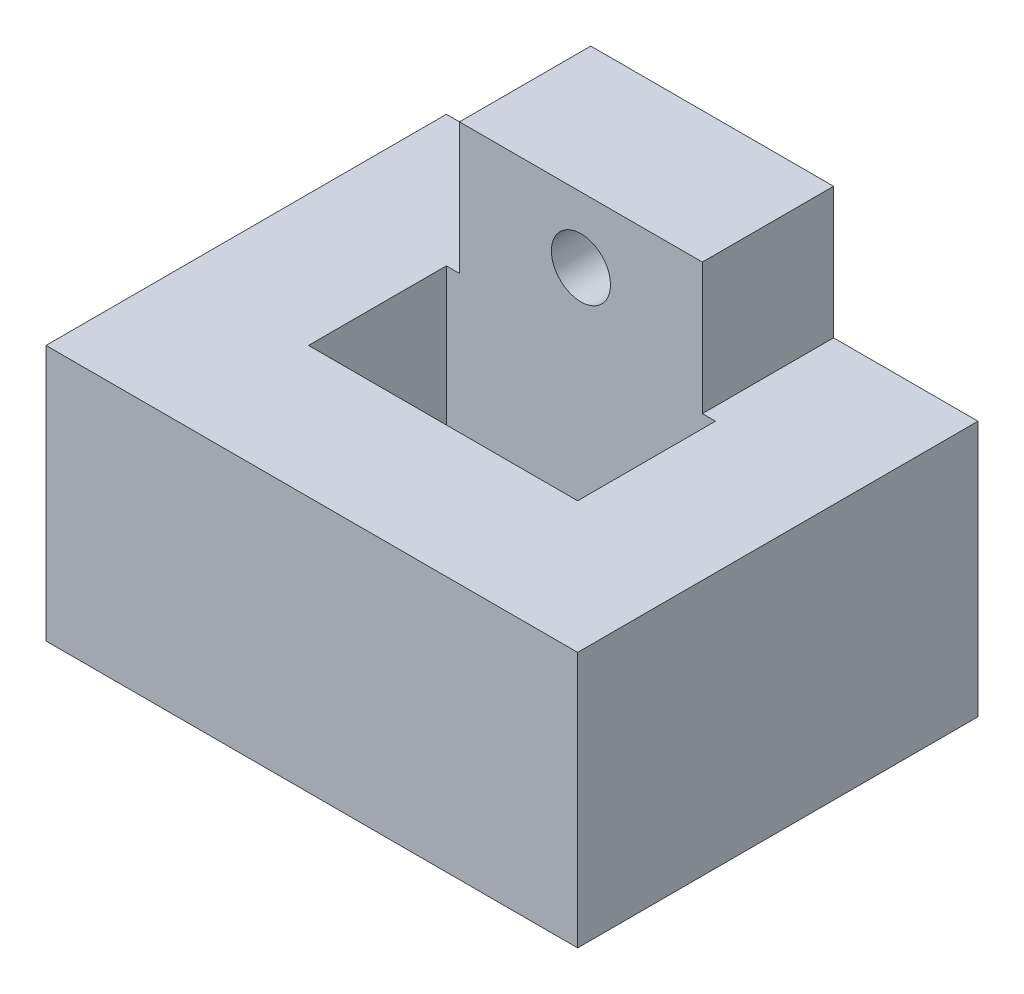
SolidWorks part; units mm, degrees
ref_plane "Front Plane" through (0, 0, 0) normal (0, 0, 1) x (1, 0, 0)
ref_plane "Top Plane" through (0, 0, 0) normal (0, 1, 0) x (1, 0, 0)
ref_plane "Right Plane" through (0, 0, 0) normal (1, 0, 0) x (0, 0, -1)
sketch "Sketch1" plane through (0, 0, 0) normal (0, 1, 0) x (1, 0, 0)
  line L1 (-10.25, 5.25) -> (10.25, 5.25)
  line L2 (-10.25, 5.25) -> (-10.25, -5.25)
  line L3 (-10.25, -5.25) -> (10.25, -5.25)
  line L4 (10.25, 5.25) -> (10.25, -5.25)
  line L5 (-10.25, 5.25) -> (10.25, -5.25) construction
  line L6 (-10.25, -5.25) -> (10.25, 5.25) construction
  line L7 (-20.25, 15.25) -> (20.25, 15.25)
  line L8 (-20.25, 15.25) -> (-20.25, -15.25)
  line L9 (-20.25, -15.25) -> (20.25, -15.25)
  line L10 (20.25, 15.25) -> (20.25, -15.25)
  line L11 (-20.25, 15.25) -> (20.25, -15.25) construction
  line L12 (-20.25, -15.25) -> (20.25, 15.25) construction
  point P0 (0, 0)
  point P6 (0, 0)
  dimension "D1" = 20.5
  dimension "D2" = 10.5
  dimension "D3" = 40.5
  dimension "D4" = 30.5
extrude "Boss-Extrude1" add sketch "Sketch1" along normal blind 19.5
sketch "Sketch4" plane through (0, 0, -15.25) normal (0, 0, 1) x (1, 0, 0)
  line L0 (0, 4.5) -> (0, 0) construction
  line L1 (-20.25, 0) -> (20.25, 0) construction
  circle A0 centre (0, 4.5) radius 1
  dimension "D2" = 2
  dimension "D1" = 4.5
extrude "Boss-Extrude2" add sketch "Sketch4" against normal blind 3
sketch "Sketch3" plane through (0, 0, -15.25) normal (0, 0, -1) x (-1, 0, 0)
  line L0 (-20.25, 19.5) -> (20.25, 19.5) construction
  line L1 (9.25, 19.5) -> (-9.25, 19.5)
  line L2 (9.25, 19.5) -> (9.25, 29.5)
  line L3 (9.25, 29.5) -> (-9.25, 29.5)
  line L4 (-9.25, 19.5) -> (-9.25, 29.5)
  line L5 (0, 24.5) -> (0, 29.5) construction
  circle A0 centre (0, 24.5) radius 2.25
  circle A1 centre (0, 4.5) radius 1 construction
  point P6 (0, 19.5)
  dimension "D4" = 4.5
  dimension "D1" = 18.5
  dimension "D2" = 10
  dimension "D3" = 20
extrude "Boss-Extrude3" add sketch "Sketch3" against normal up to surface (10 mm away) up to face at (0, 9.75, -5.25)
